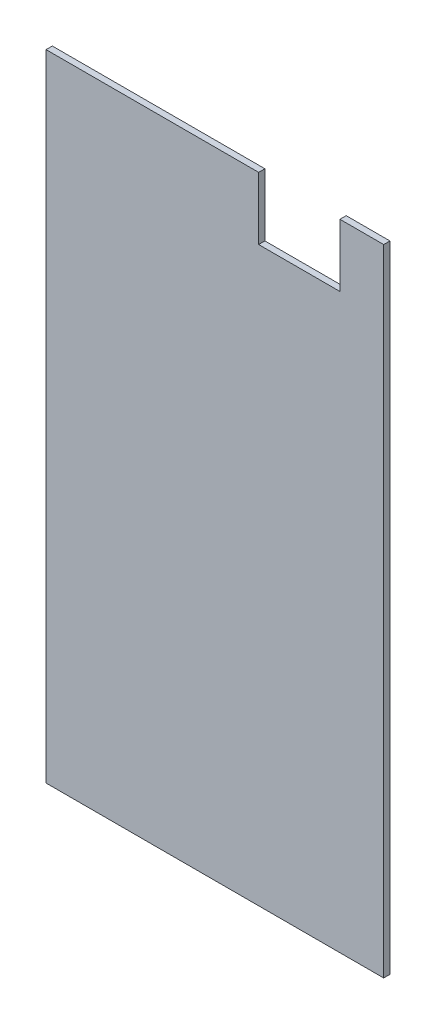
SolidWorks part; units mm, degrees
ref_plane "Front Plane" through (0, 0, 0) normal (0, 0, 1) x (1, 0, 0)
ref_plane "Top Plane" through (0, 0, 0) normal (0, 1, 0) x (1, 0, 0)
ref_plane "Right Plane" through (0, 0, 0) normal (1, 0, 0) x (0, 0, -1)
sketch "Sketch1" plane through (0, 0, 0) normal (0, 0, 1) x (1, 0, 0)
  line L1 (-40.5, 76.2) -> (40.5, 76.2)
  line L2 (-40.5, 76.2) -> (-40.5, -76.2)
  line L3 (-40.5, -76.2) -> (40.5, -76.2)
  line L4 (40.5, 76.2) -> (40.5, -76.2)
  line L5 (-40.5, 76.2) -> (40.5, -76.2) construction
  line L6 (-40.5, -76.2) -> (40.5, 76.2) construction
  point P0 (0, 0)
  dimension "D1" = 81
  dimension "D2" = 152.4
extrude "Boss-Extrude1" add sketch "Sketch1" along normal blind 1.5
sketch "Sketch3" plane through (0, 0, 1.5) normal (0, 0, 1) x (1, 0, 0)
  line L0 (40.5, 76.2) -> (30, 76.2)
  line L1 (40.5, 76.2) -> (-40.5, 76.2) construction
  line L2 (30, 76.2) -> (30, 61.2)
  line L3 (30, 61.2) -> (10.5, 61.2)
  line L4 (10.5, 61.2) -> (10.5, 76.2)
  line L5 (10.5, 76.2) -> (30, 76.2)
  line M7 (40.5, 76.2) -> (-40.5, 76.2)
extrude "Cut-Extrude1" cut sketch "Sketch3" against normal blind 10 contours L4 L3 L2 M7
